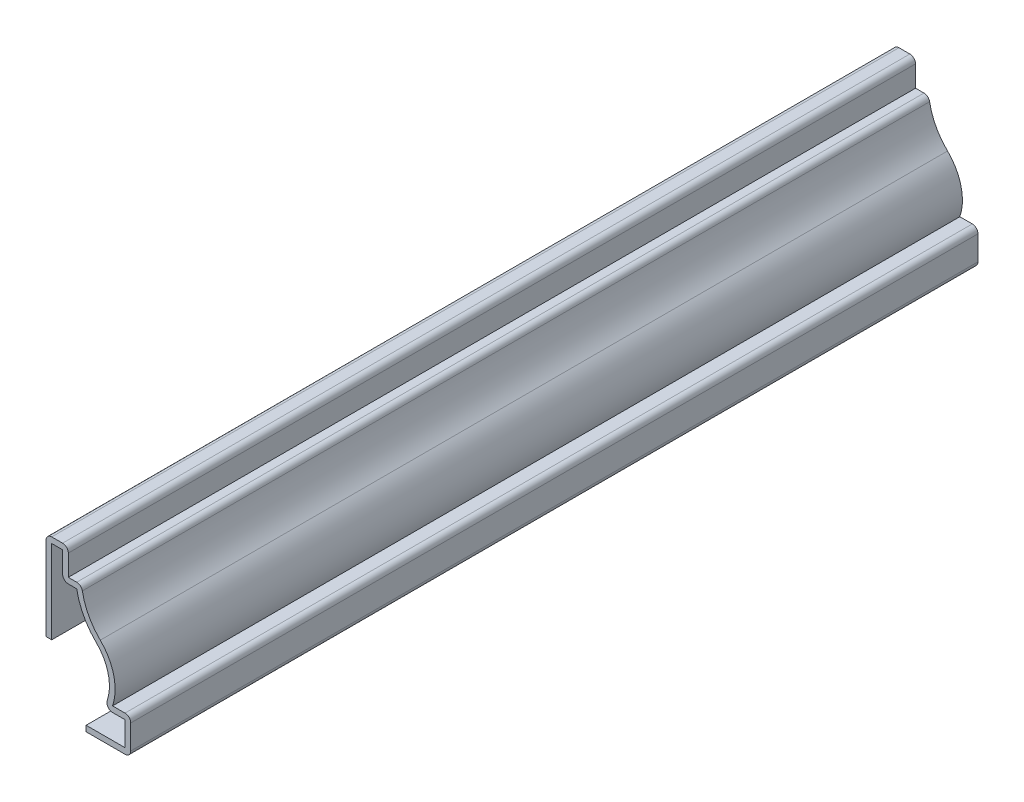
SolidWorks part; units mm, degrees
ref_plane "Front Plane" through (0, 0, 0) normal (0, 0, 1) x (1, 0, 0)
ref_plane "Top Plane" through (0, 0, 0) normal (0, 1, 0) x (1, 0, 0)
ref_plane "Right Plane" through (0, 0, 0) normal (1, 0, 0) x (0, 0, -1)
sketch "Sketch1" plane through (0, 0, 0) normal (0, 0, 1) x (1, 0, 0)
  line L0 (0, 0) -> (0, 23.1736) construction
  line L1 (-11.9062, 0) -> (-19.8438, 0) construction
  line L2 (-19.8438, 0) -> (-19.8438, 6.35) construction
  line L3 (-19.8438, 6.35) -> (-16.6119, 6.35) construction
  line L4 (-11.1125, 22.225) -> (-8.7313, 22.225) construction
  line L5 (-8.7313, 22.225) -> (-8.7313, 26.9875) construction
  line L6 (-8.7313, 26.9875) -> (-4.7625, 26.9875) construction
  line L7 (-4.7625, 26.9875) -> (-4.7625, 11.1125) construction
  line L9 (4.7625, 26.9875) -> (4.7625, 11.1125)
  line L10 (8.7313, 26.9875) -> (4.7625, 26.9875)
  line L11 (8.7313, 22.225) -> (8.7313, 26.9875)
  line L12 (11.1125, 22.225) -> (8.7313, 22.225)
  line L13 (19.8438, 6.35) -> (16.6119, 6.35)
  line L14 (19.8438, 0) -> (19.8438, 6.35)
  line L15 (11.9062, 0) -> (19.8438, 0)
  arc A0 (-16.6119, 6.35) -> (-14.4209, 15.3883) centre (-8.3344, 9.1281) cw construction
  arc A1 (-14.4209, 15.3883) -> (-11.1125, 22.225) centre (-22.1673, 23.3557) ccw construction
  arc A2 (14.4209, 15.3883) -> (11.1125, 22.225) centre (22.1673, 23.3557) cw
  arc A3 (16.6119, 6.35) -> (14.4209, 15.3883) centre (8.3344, 9.1281) ccw
  point P31 (0, 11.1125)
extrude "Extrude-Thin1" add sketch "Sketch1" against normal blind 150.8125 thin thin type one direction reverse wall 1.016
fillet "Fillet1" radius 1.016 7 edges at (15.0522, 5.334, -75.4062) (19.8438, 0, -75.4062) (19.8438, 6.35, -75.4062) (11.1125, 22.225, -75.4062) (7.7153, 21.209, -75.4062) (8.7313, 26.9875, -75.4062) (4.7625, 26.9875, -75.4062)
equation "\"D1@Extrude-Thin1\"=\"D6@Sketch1\"*10"
